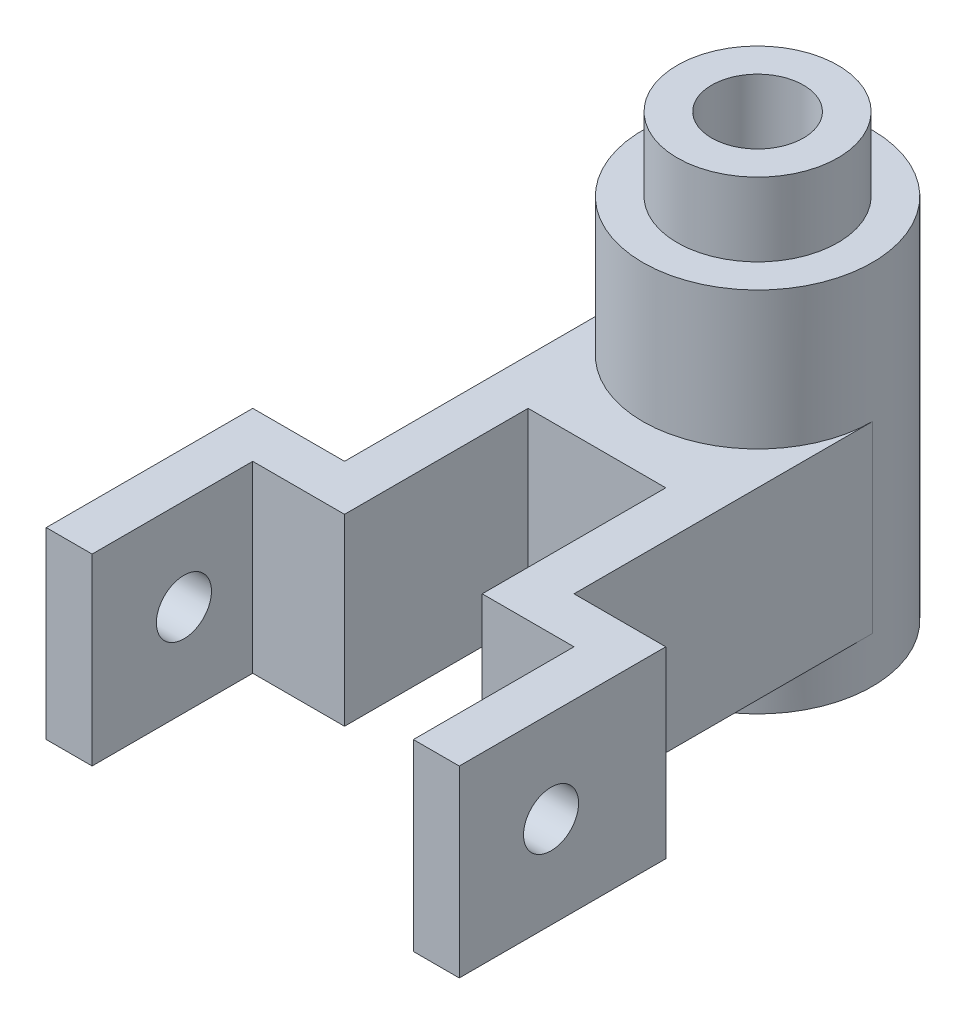
SolidWorks part; units mm, degrees
ref_plane "Front Plane" through (0, 0, 0) normal (0, 0, 1) x (1, 0, 0)
ref_plane "Top Plane" through (0, 0, 0) normal (0, 1, 0) x (1, 0, 0)
ref_plane "Right Plane" through (0, 0, 0) normal (1, 0, 0) x (0, 0, -1)
sketch "Sketch1" plane through (0, 0, 0) normal (0, 1, 0) x (1, 0, 0)
  circle A0 centre (0, 0) radius 25
  dimension "D1" = 50
extrude "Boss-Extrude1" add sketch "Sketch1" along normal blind 80
sketch "Sketch2" plane through (0, 80, 0) normal (0, 1, 0) x (1, 0, 0)
  circle A0 centre (0, 0) radius 17.5
  dimension "D1" = 35
extrude "Boss-Extrude2" add sketch "Sketch2" along normal blind 16 contours A0
sketch "Sketch3" plane through (0, 96, 0) normal (0, 1, 0) x (1, 0, 0)
  circle A0 centre (0, 0) radius 10
  dimension "D1" = 20
extrude "Cut-Extrude1" cut sketch "Sketch3" against normal blind 200
sketch "Sketch4" plane through (0, 0, 0) normal (0, 1, 0) x (1, 0, 0)
  line L0 (0, 0) -> (0, -132.4347) construction
  line L1 (-25, 0) -> (-25, -65)
  line L2 (-25, -65) -> (-45, -65)
  line L3 (-45, -65) -> (-45, -110)
  line L4 (-45, -110) -> (-35, -110)
  line L5 (-15, -35) -> (-15, -75)
  line L6 (-15, -75) -> (-35, -75)
  line L7 (-35, -75) -> (-35, -110)
  line L8 (-35, -100) -> (-35, -100)
  line L9 (-35, -75) -> (-35, -100) construction
  line L10 (-15, 0) -> (-15, -75) construction
  line L11 (-15, -35) -> (0, -35)
  line L12 (25, 0) -> (25, -65)
  line L13 (15, -35) -> (0, -35)
  line L14 (35, -75) -> (35, -110)
  line L15 (15, -75) -> (35, -75)
  line L16 (15, -35) -> (15, -75)
  line L17 (45, -110) -> (35, -110)
  line L18 (45, -65) -> (45, -110)
  line L19 (25, -65) -> (45, -65)
  circle A0 centre (0, 0) radius 25 construction
  arc A2 (-25, 0) -> (25, 0) centre (0, 0) ccw
  point P15 (-7.5, -35)
  dimension "D1" = 65
  dimension "D2" = 20
  dimension "D3" = 25
  dimension "D4" = 45
  dimension "D5" = 10
  dimension "D7" = 35
  dimension "D6" = 10
extrude "Boss-Extrude3" add sketch "Sketch4" along normal blind 40 from offset 10 contours L14 L17 L18 L19 L12 A2 L1 L2 L3 L4 L7 L6 L5 L11 L13 L16 L15
sketch "Sketch5" plane through (45, 0, 0) normal (1, 0, 0) x (0, 0, -1)
  line L0 (-110, 50) -> (-110, 10) construction
  line L1 (-65, 10) -> (-110, 10) construction
  circle A0 centre (-90, 30) radius 6
  point P2 (0, 0)
  dimension "D3" = 12
  dimension "D1" = 20
  dimension "D2" = 20
extrude "Cut-Extrude2" cut sketch "Sketch5" against normal blind 100
